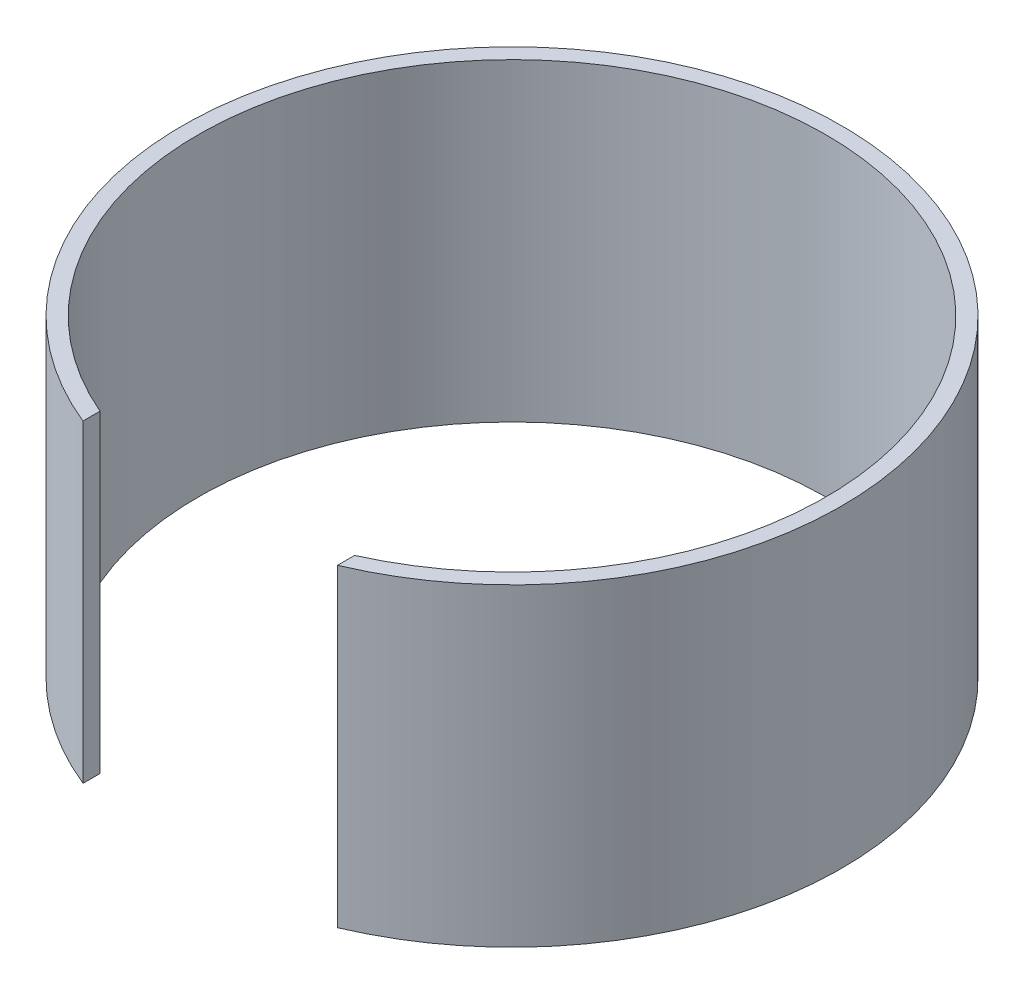
SolidWorks part; units mm, degrees
ref_plane "Front Plane" through (0, 0, 0) normal (0, 0, 1) x (1, 0, 0)
ref_plane "Top Plane" through (0, 0, 0) normal (0, 1, 0) x (1, 0, 0)
ref_plane "Right Plane" through (0, 0, 0) normal (1, 0, 0) x (0, 0, -1)
sketch "Sketch1" plane through (0, 0, 0) normal (0, 1, 0) x (1, 0, 0)
  line L0 (0, 0) -> (-0.9196, 104.996) construction
  line L3 (-0.9196, 104.996) -> (1.062, -121.2655) construction
  line L4 (1.062, -121.2655) -> (-66.0502, 0) construction
  line L6 (0, 0) -> (-37.4578, -92.7196) construction
  line L7 (-39.3307, -97.3555) -> (-39.3307, -91.9407)
  line L8 (41.0298, -96.6517) -> (41.0298, -91.1952)
  arc A0 (41.0298, -96.6517) -> (-39.3307, -97.3555) centre (0, 0) ccw
  arc A1 (41.0298, -91.1952) -> (-39.3307, -91.9407) centre (0, 0) ccw
  dimension "D1" = 200
  dimension "D2" = 210
  dimension "D3" = 80.3635
extrude "Boss-Extrude1" add sketch "Sketch1" along normal blind 100
